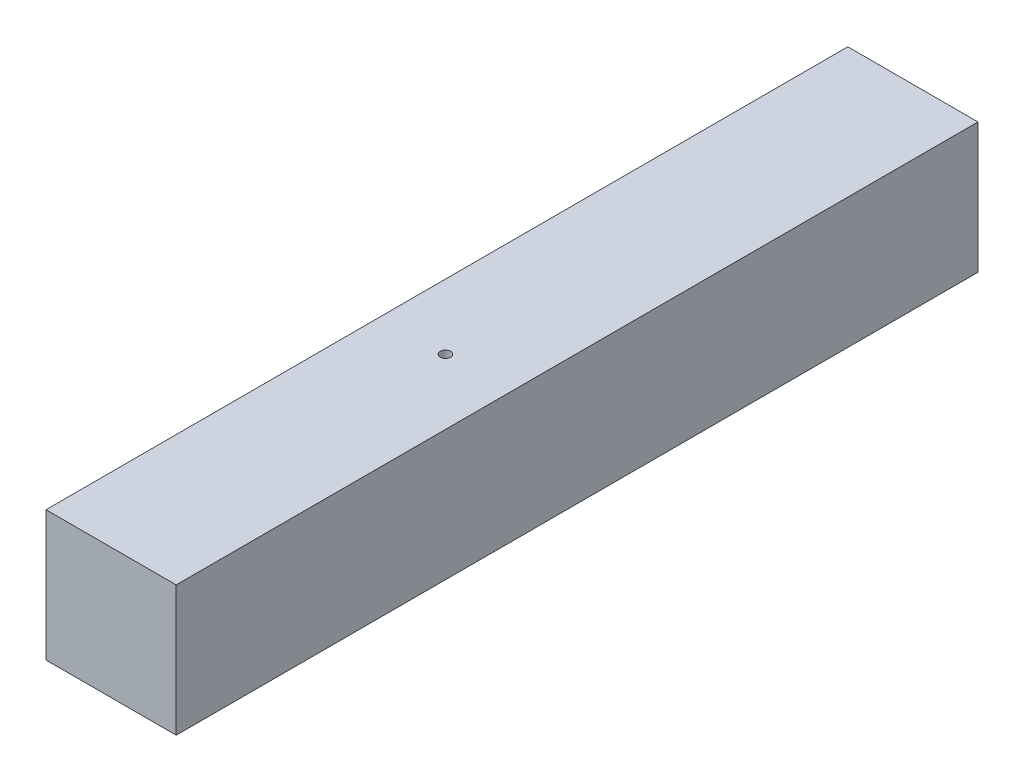
SolidWorks part; units mm, degrees
material "Pin"
ref_plane "Plan de face" through (0, 0, 0) normal (0, 0, 1) x (1, 0, 0)
ref_plane "Plan de dessus" through (0, 0, 0) normal (0, 1, 0) x (1, 0, 0)
ref_plane "Plan de droite" through (0, 0, 0) normal (1, 0, 0) x (0, 0, -1)
sketch "Esquisse1" plane through (0, 0, 0) normal (0, 0, 1) x (1, 0, 0)
  line L1 (22, 22) -> (-22, 22)
  line L2 (22, 22) -> (22, -22)
  line L3 (22, -22) -> (-22, -22)
  line L4 (-22, 22) -> (-22, -22)
  line L5 (22, 22) -> (-22, -22) construction
  line L6 (22, -22) -> (-22, 22) construction
  point P0 (0, 0)
extrude "Boss.-Extru.1" add sketch "Esquisse1" along normal blind 271
sketch "Esquisse2" plane through (0, -22, 0) normal (0, -1, 0) x (1, 0, 0)
  circle A0 centre (0, 158) radius 1.75
  dimension "D1" = 3.5
  dimension "D2" = 158
extrude "Enlèv. mat.-Extru.1" cut sketch "Esquisse2" against normal up to surface (44 mm away) up to face at (0, 22, 135.5)
sketch "Esquisse3" plane through (0, 0, 0) normal (0, 0, -1) x (-1, 0, 0)
  circle A0 centre (0, 0) radius 1.75
  dimension "D1" = 3.5
extrude "Enlèv. mat.-Extru.2" cut sketch "Esquisse3" against normal blind 60
